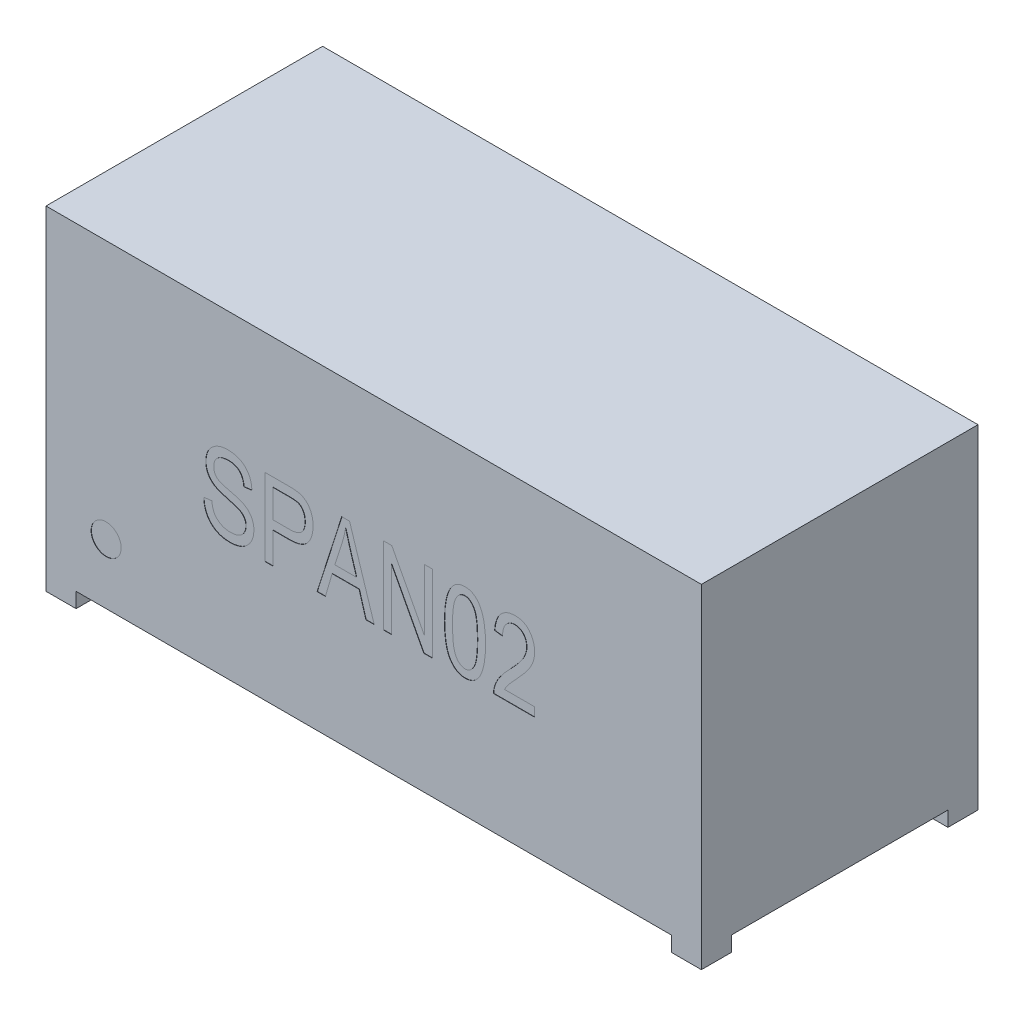
SolidWorks part; units mm, degrees
ref_plane "Front Plane" through (0, 0, 0) normal (0, 0, 1) x (1, 0, 0)
ref_plane "Top Plane" through (0, 0, 0) normal (0, 1, 0) x (1, 0, 0)
ref_plane "Right Plane" through (0, 0, 0) normal (1, 0, 0) x (0, 0, -1)
sketch "Sketch1" plane through (0, 0, 0) normal (0, 1, 0) x (1, 0, 0)
  line L1 (10.9, -4.6) -> (-10.9, -4.6)
  line L2 (10.9, -4.6) -> (10.9, 4.6)
  line L3 (10.9, 4.6) -> (-10.9, 4.6)
  line L4 (-10.9, -4.6) -> (-10.9, 4.6)
  line L5 (10.9, -4.6) -> (-10.9, 4.6) construction
  line L6 (10.9, 4.6) -> (-10.9, -4.6) construction
  point P0 (0, 0)
  dimension "D1" = 21.8
  dimension "D2" = 9.2
extrude "Boss-Extrude1" add sketch "Sketch1" along normal blind 11.1
sketch "Sketch2" plane through (0, 0, 0) normal (0, -1, 0) x (1, 0, 0)
  line L0 (-9.9, 4.6) -> (9.9, 4.6)
  line L1 (-10.9, 4.6) -> (10.9, 4.6) construction
  line L2 (9.9, 4.6) -> (9.9, 3.6)
  line L3 (9.9, 3.6) -> (10.9, 3.6)
  line L4 (10.9, 4.6) -> (10.9, -4.6) construction
  line L5 (10.9, 3.6) -> (10.9, -3.6)
  line L6 (10.9, -3.6) -> (9.9, -3.6)
  line L7 (9.9, -3.6) -> (9.9, -4.6)
  line L8 (10.9, -4.6) -> (-10.9, -4.6) construction
  line L9 (9.9, -4.6) -> (-9.9, -4.6)
  line L10 (-9.9, -4.6) -> (-9.9, -3.6)
  line L11 (-9.9, -3.6) -> (-10.9, -3.6)
  line L12 (-10.9, -4.6) -> (-10.9, 4.6) construction
  line L13 (-10.9, -3.6) -> (-10.9, 3.6)
  line L14 (-10.9, 3.6) -> (-9.9, 3.6)
  line L15 (-9.9, 3.6) -> (-9.9, 4.6)
  dimension "D1" = 1
  dimension "D2" = 1
extrude "Cut-Extrude1" cut sketch "Sketch2" against normal blind 0.5
sketch "Sketch3" plane through (0, 0, 4.6) normal (0, 0, 1) x (1, 0, 0)
  line L0 (-8.9, -4.265) -> (-8.9, -3.935) construction
  line L1 (9.9, 0.5) -> (-9.9, 0.5) construction
  circle A0 centre (-8.9, 2.5) radius 0.5
  dimension "D1" = 1
  dimension "D2" = 2
extrude "Cut-Extrude2" cut sketch "Sketch3" against normal blind 0.01
sketch "Sketch5" plane through (0, 0, 4.6) normal (0, 0, 1) x (1, 0, 0)
  line L0 (-5.8196, 4.5) -> (5.8196, 4.5) construction
  line L1 (0, -5.06) -> (0, 5.06) construction
  line L2 (9.9, 0.5) -> (-9.9, 0.5) construction
  text T0 "SPAN02" font "Arial Narrow" height in points 10
  point P4 (0, 4.5)
  dimension "D1" = 4
extrude "Cut-Extrude3" cut sketch "Sketch5" against normal blind 0.01
ref_plane "Plane1" through (0, 0, -1.1) normal (0, 0, 1) x (1, 0, 0)
